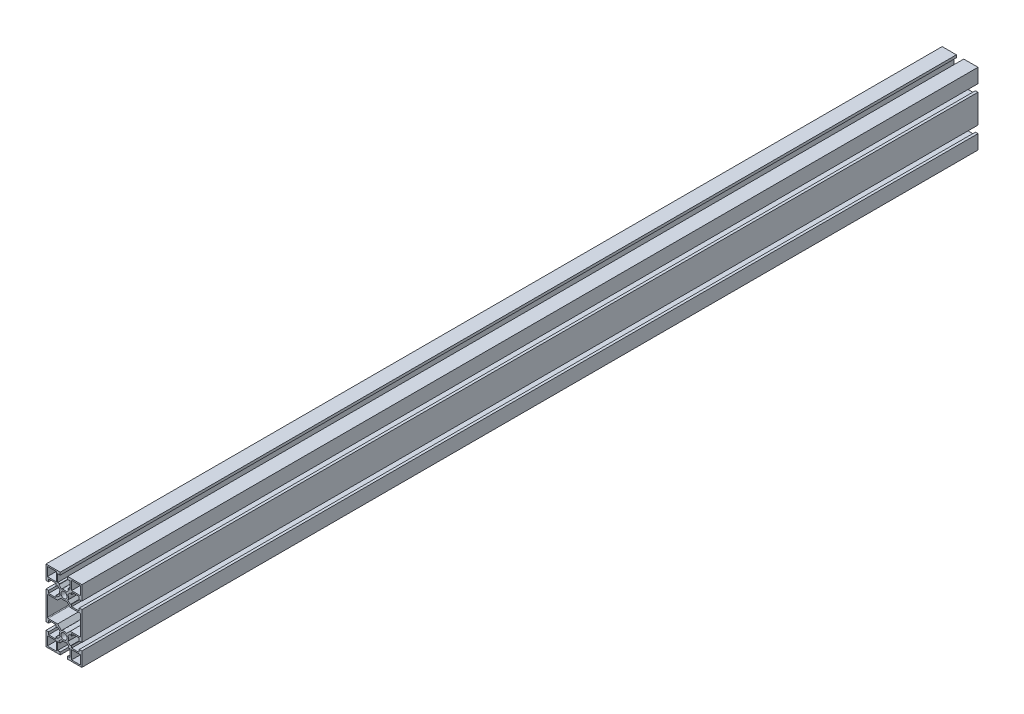
SolidWorks part; units mm, degrees
material "6063 T5"
ref_plane "Спереди" through (0, 0, 0) normal (0, 0, 1) x (1, 0, 0)
ref_plane "Сверху" through (0, 0, 0) normal (0, 1, 0) x (1, 0, 0)
ref_plane "Справа" through (0, 0, 0) normal (1, 0, 0) x (0, 0, -1)
sketch "Эскиз1" plane through (0, 0, 0) normal (0, 0, 1) x (1, 0, 0)
  line L0 (-27.6903, 39.9641) -> (-27.6903, -40.0359) construction
  line L1 (0, 20) -> (0, -20) construction
  line L2 (0, 0) -> (27.4171, 0) construction
  line L3 (-20, 27) -> (-20, 40)
  line L4 (-20, 40) -> (-7, 40)
  line L5 (7, 40) -> (20, 40)
  line L6 (20, 40) -> (20, 27)
  line L7 (18.5, 28.5) -> (8.5, 28.5)
  line L8 (-18.5, 38.5) -> (-8.5, 38.5)
  line L9 (-18.5, 38.5) -> (-18.5, 28.5)
  line L10 (-18.5, 28.5) -> (-8.5, 28.5)
  line L11 (-8.5, 38.5) -> (-8.5, 28.5)
  line L12 (8.5, 38.5) -> (8.5, 28.5)
  line L13 (18.5, 38.5) -> (8.5, 38.5)
  line L14 (18.5, 38.5) -> (18.5, 28.5)
  line L15 (18.5, -38.5) -> (18.5, -28.5)
  line L16 (18.5, -38.5) -> (8.5, -38.5)
  line L17 (8.5, -38.5) -> (8.5, -28.5)
  line L18 (-8.5, -38.5) -> (-8.5, -28.5)
  line L19 (-18.5, -28.5) -> (-8.5, -28.5)
  line L20 (-18.5, -38.5) -> (-18.5, -28.5)
  line L21 (-18.5, -38.5) -> (-8.5, -38.5)
  line L22 (18.5, -28.5) -> (8.5, -28.5)
  line L23 (20, -40) -> (20, -27)
  line L24 (7, -40) -> (20, -40)
  line L25 (-20, -40) -> (-7, -40)
  line L26 (-20, -27) -> (-20, -40)
  line L27 (-20, 13) -> (-20, -13)
  line L28 (20, 13) -> (20, -13)
  line L29 (-17.7, 11.5) -> (-7.0858, 11.5)
  line L30 (-7.0858, 11.5) -> (-2.8291, 15.7567)
  line L31 (-18.5, 10.7) -> (-18.5, -10.7)
  line L32 (7.0858, 11.5) -> (2.8291, 15.7567)
  line L33 (17.7, 11.5) -> (7.0858, 11.5)
  line L34 (18.5, 10.7) -> (18.5, -10.7)
  line L35 (-17.7, -11.5) -> (-7.0858, -11.5)
  line L36 (-7.0858, -11.5) -> (-2.8291, -15.7567)
  line L37 (7.0858, -11.5) -> (2.8291, -15.7567)
  line L38 (17.7, -11.5) -> (7.0858, -11.5)
  arc A0 (-2.8291, 15.7567) -> (2.8291, 15.7567) centre (0, 20) ccw
  arc A1 (-17.7, 11.5) -> (-18.5, 10.7) centre (-17.7, 10.7) ccw
  arc A2 (17.7, 11.5) -> (18.5, 10.7) centre (17.7, 10.7) cw
  arc A3 (-17.7, -11.5) -> (-18.5, -10.7) centre (-17.7, -10.7) cw
  arc A4 (-2.8291, -15.7567) -> (2.8291, -15.7567) centre (0, -20) cw
  arc A5 (17.7, -11.5) -> (18.5, -10.7) centre (17.7, -10.7) ccw
  circle A6 centre (0, 20) radius 3.4
  circle A7 centre (0, -20) radius 3.4
  point P8 (0, 20)
  point P21 (0, -20)
  point P55 (-18.5, 11.5)
  point P69 (-18.5, 0)
  point P71 (18.5, 0)
  line B0 (-20, 24.1) -> (-17.1, 24.1)
  line B1 (-17.1, 24.1) -> (-17.1, 27)
  line B2 (-17.1, 27) -> (-8.6, 27)
  line B3 (-8.6, 27) -> (-8.6, 24.5824)
  line B4 (-8.2586, 24.441) -> (-7.1276, 25.572)
  line B5 (-7.1276, 25.572) -> (-4.2992, 22.7435)
  line B6 (0, 20) -> (-20, 20) construction
  line B7 (-20, 24.1) -> (-20, 27)
  line B8 (-20, 15.9) -> (-20, 13)
  line B9 (-7.1276, 14.428) -> (-4.2992, 17.2565)
  line B10 (-8.2586, 15.559) -> (-7.1276, 14.428)
  line B11 (-8.6, 13) -> (-8.6, 15.4176)
  line B12 (-17.1, 13) -> (-8.6, 13)
  line B13 (-17.1, 15.9) -> (-17.1, 13)
  line B14 (-20, 15.9) -> (-17.1, 15.9)
  arc B15 (-4.2992, 22.7435) -> (-4.2992, 17.2565) centre (0, 20) ccw
  arc B16 (-8.6, 24.5824) -> (-8.2586, 24.441) centre (-8.4, 24.5824) ccw
  arc B17 (-8.6, 15.4176) -> (-8.2586, 15.559) centre (-8.4, 15.4176) cw
  line B18 (4.1, 40) -> (4.1, 37.1)
  line B19 (4.1, 37.1) -> (7, 37.1)
  line B20 (7, 37.1) -> (7, 28.6)
  line B21 (7, 28.6) -> (4.5824, 28.6)
  line B22 (4.441, 28.2586) -> (5.572, 27.1276)
  line B23 (5.572, 27.1276) -> (2.7435, 24.2992)
  line B24 (0, 20) -> (0, 40) construction
  line B25 (4.1, 40) -> (7, 40)
  line B26 (-4.1, 40) -> (-7, 40)
  line B27 (-5.572, 27.1276) -> (-2.7435, 24.2992)
  line B28 (-4.441, 28.2586) -> (-5.572, 27.1276)
  line B29 (-7, 28.6) -> (-4.5824, 28.6)
  line B30 (-7, 37.1) -> (-7, 28.6)
  line B31 (-4.1, 37.1) -> (-7, 37.1)
  line B32 (-4.1, 40) -> (-4.1, 37.1)
  arc B33 (2.7435, 24.2992) -> (-2.7435, 24.2992) centre (0, 20) ccw
  arc B34 (4.5824, 28.6) -> (4.441, 28.2586) centre (4.5824, 28.4) ccw
  arc B35 (-4.5824, 28.6) -> (-4.441, 28.2586) centre (-4.5824, 28.4) cw
  line B36 (20, 15.9) -> (17.1, 15.9)
  line B37 (17.1, 15.9) -> (17.1, 13)
  line B38 (17.1, 13) -> (8.6, 13)
  line B39 (8.6, 13) -> (8.6, 15.4176)
  line B40 (8.2586, 15.559) -> (7.1276, 14.428)
  line B41 (7.1276, 14.428) -> (4.2992, 17.2565)
  line B42 (0, 20) -> (20, 20) construction
  line B43 (20, 15.9) -> (20, 13)
  line B44 (20, 24.1) -> (20, 27)
  line B45 (7.1276, 25.572) -> (4.2992, 22.7435)
  line B46 (8.2586, 24.441) -> (7.1276, 25.572)
  line B47 (8.6, 27) -> (8.6, 24.5824)
  line B48 (17.1, 27) -> (8.6, 27)
  line B49 (17.1, 24.1) -> (17.1, 27)
  line B50 (20, 24.1) -> (17.1, 24.1)
  arc B51 (4.2992, 17.2565) -> (4.2992, 22.7435) centre (0, 20) ccw
  arc B52 (8.6, 15.4176) -> (8.2586, 15.559) centre (8.4, 15.4176) ccw
  arc B53 (8.6, 24.5824) -> (8.2586, 24.441) centre (8.4, 24.5824) cw
  line B54 (-20, -24.1) -> (-17.1, -24.1)
  line B55 (-17.1, -24.1) -> (-17.1, -27)
  line B56 (-17.1, -27) -> (-8.6, -27)
  line B57 (-8.6, -27) -> (-8.6, -24.5824)
  line B58 (-8.2586, -24.441) -> (-7.1276, -25.572)
  line B59 (-7.1276, -25.572) -> (-4.2992, -22.7435)
  line B60 (0, -20) -> (-20, -20) construction
  line B61 (-20, -24.1) -> (-20, -27)
  line B62 (-20, -15.9) -> (-20, -13)
  line B63 (-7.1276, -14.428) -> (-4.2992, -17.2565)
  line B64 (-8.2586, -15.559) -> (-7.1276, -14.428)
  line B65 (-8.6, -13) -> (-8.6, -15.4176)
  line B66 (-17.1, -13) -> (-8.6, -13)
  line B67 (-17.1, -15.9) -> (-17.1, -13)
  line B68 (-20, -15.9) -> (-17.1, -15.9)
  arc B69 (-4.2992, -22.7435) -> (-4.2992, -17.2565) centre (0, -20) cw
  arc B70 (-8.6, -24.5824) -> (-8.2586, -24.441) centre (-8.4, -24.5824) cw
  arc B71 (-8.6, -15.4176) -> (-8.2586, -15.559) centre (-8.4, -15.4176) ccw
  line B72 (20, -15.9) -> (17.1, -15.9)
  line B73 (17.1, -15.9) -> (17.1, -13)
  line B74 (17.1, -13) -> (8.6, -13)
  line B75 (8.6, -13) -> (8.6, -15.4176)
  line B76 (8.2586, -15.559) -> (7.1276, -14.428)
  line B77 (7.1276, -14.428) -> (4.2992, -17.2565)
  line B78 (0, -20) -> (20, -20) construction
  line B79 (20, -15.9) -> (20, -13)
  line B80 (20, -24.1) -> (20, -27)
  line B81 (7.1276, -25.572) -> (4.2992, -22.7435)
  line B82 (8.2586, -24.441) -> (7.1276, -25.572)
  line B83 (8.6, -27) -> (8.6, -24.5824)
  line B84 (17.1, -27) -> (8.6, -27)
  line B85 (17.1, -24.1) -> (17.1, -27)
  line B86 (20, -24.1) -> (17.1, -24.1)
  arc B87 (4.2992, -17.2565) -> (4.2992, -22.7435) centre (0, -20) cw
  arc B88 (8.6, -15.4176) -> (8.2586, -15.559) centre (8.4, -15.4176) cw
  arc B89 (8.6, -24.5824) -> (8.2586, -24.441) centre (8.4, -24.5824) ccw
  line B90 (4.1, -40) -> (4.1, -37.1)
  line B91 (4.1, -37.1) -> (7, -37.1)
  line B92 (7, -37.1) -> (7, -28.6)
  line B93 (7, -28.6) -> (4.5824, -28.6)
  line B94 (4.441, -28.2586) -> (5.572, -27.1276)
  line B95 (5.572, -27.1276) -> (2.7435, -24.2992)
  line B96 (0, -20) -> (0, -40) construction
  line B97 (4.1, -40) -> (7, -40)
  line B98 (-4.1, -40) -> (-7, -40)
  line B99 (-5.572, -27.1276) -> (-2.7435, -24.2992)
  line B100 (-4.441, -28.2586) -> (-5.572, -27.1276)
  line B101 (-7, -28.6) -> (-4.5824, -28.6)
  line B102 (-7, -37.1) -> (-7, -28.6)
  line B103 (-4.1, -37.1) -> (-7, -37.1)
  line B104 (-4.1, -40) -> (-4.1, -37.1)
  arc B105 (2.7435, -24.2992) -> (-2.7435, -24.2992) centre (0, -20) cw
  arc B106 (4.5824, -28.6) -> (4.441, -28.2586) centre (4.5824, -28.4) cw
  arc B107 (-4.5824, -28.6) -> (-4.441, -28.2586) centre (-4.5824, -28.4) ccw
  dimension "D8" = 1.5
  dimension "D11" = 0.8
  dimension "D12" = 6.8
  dimension "D1" = 80
  dimension "D2" = 40
  dimension "D3" = 20
  dimension "D4" = 3
  dimension "D5" = 1.5
  dimension "D6" = 1.5
  dimension "D7" = 10
  dimension "D9" = 11.5
  dimension "D10" = 2.1
sketch_block_instance "Блок1-1"
sketch_block "Блок1" parameters "D7"=5.1, "D10"=0.2, "D1"=14, "D2"=8.2, "D3"=2.9, "D4"=11.4, "D5"=20, "D6"=45, "D8"=1.1, "D9"=4
sketch_block_instance "Блок1-2"
sketch_block_instance "Блок1-3"
sketch_block_instance "Блок1-4"
sketch_block_instance "Блок1-5"
sketch_block_instance "Блок1-6"
extrude "Бобышка-Вытянуть1" add sketch "Эскиз1" along normal blind 1000 contours B101 B107 B100 B99 B105 B95 B94 B106 B93 B92 B91 B90 B97 L24 L23 B80 B86 B85 B84 B83 B89 B82 B81 B87 B77 B76 B88 B75 B74 B73 B72 B79 L28 B43 B36 B37 B38 B39 B52 B40 B41 B51 B45 B46 B53 B47 B48 B49 B50 B44 L6
